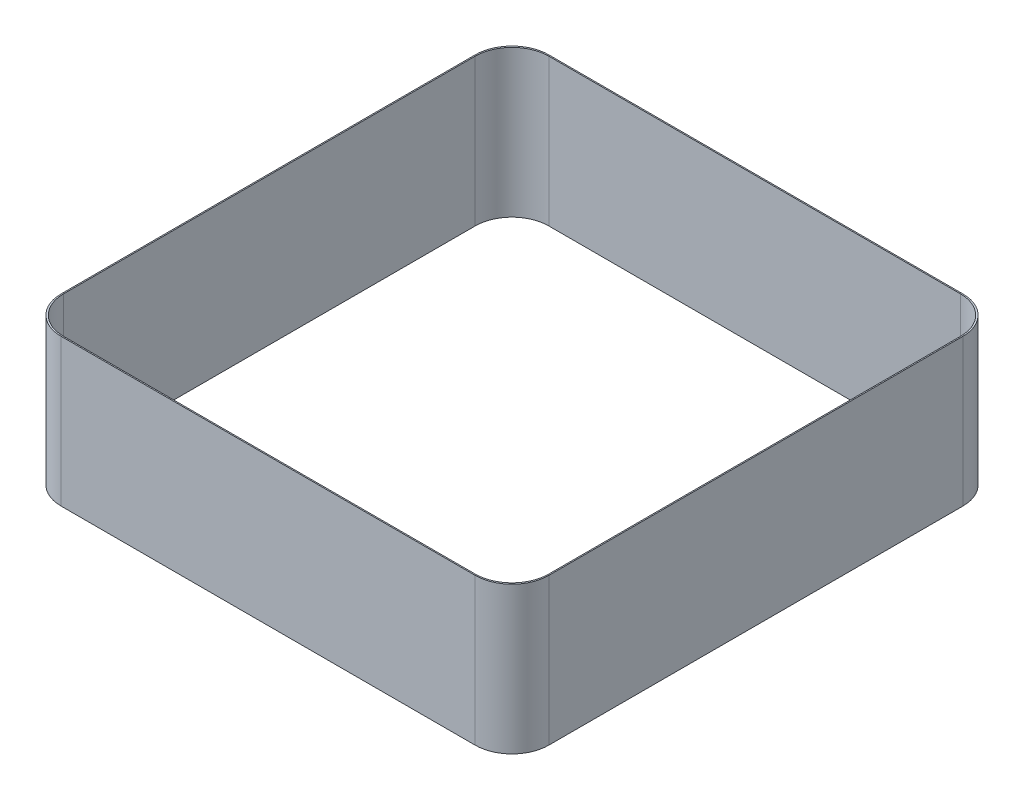
SolidWorks part; units mm, degrees
material "C110 COPPER"
ref_plane "Front Plane" through (0, 0, 0) normal (0, 0, 1) x (1, 0, 0)
ref_plane "Top Plane" through (0, 0, 0) normal (0, 1, 0) x (1, 0, 0)
ref_plane "Right Plane" through (0, 0, 0) normal (1, 0, 0) x (0, 0, -1)
sketch "Sketch2" plane through (0, 0, 0) normal (0, 1, 0) x (1, 0, 0)
  line L1 (-8.89, -10.4775) -> (8.89, -10.4775)
  line L2 (-10.4775, -8.89) -> (-10.4775, 8.89)
  line L3 (-8.89, 10.4775) -> (8.89, 10.4775)
  line L4 (10.4775, -8.89) -> (10.4775, 8.89)
  line L5 (-10.4775, -10.4775) -> (10.4775, 10.4775) construction
  line L6 (-10.4775, 10.4775) -> (10.4775, -10.4775) construction
  line L7 (-8.9408, -10.5283) -> (8.9408, -10.5283)
  line L8 (-10.5283, -8.9408) -> (-10.5283, 8.9408)
  line L9 (-8.9408, 10.5283) -> (8.9408, 10.5283)
  line L10 (10.5283, -8.9408) -> (10.5283, 8.9408)
  line L11 (-10.5283, -10.5283) -> (10.5283, 10.5283) construction
  line L12 (-10.5283, 10.5283) -> (10.5283, -10.5283) construction
  arc A0 (-8.9408, -10.5283) -> (-10.5283, -8.9408) centre (-8.9408, -8.9408) cw
  arc A1 (8.9408, -10.5283) -> (10.5283, -8.9408) centre (8.9408, -8.9408) ccw
  arc A2 (8.9408, 10.5283) -> (10.5283, 8.9408) centre (8.9408, 8.9408) cw
  arc A3 (-10.5283, 8.9408) -> (-8.9408, 10.5283) centre (-8.9408, 8.9408) cw
  arc A4 (-10.4775, 8.89) -> (-8.89, 10.4775) centre (-8.89, 8.89) cw
  arc A5 (-8.89, -10.4775) -> (-10.4775, -8.89) centre (-8.89, -8.89) cw
  arc A6 (8.89, -10.4775) -> (10.4775, -8.89) centre (8.89, -8.89) ccw
  arc A7 (8.89, 10.4775) -> (10.4775, 8.89) centre (8.89, 8.89) cw
  point P0 (0, 0)
  point P5 (0, 0)
  dimension "D3" = 1.5875
  dimension "D1" = 20.955
  dimension "D2" = 0.0508
extrude "Boss-Extrude1" add sketch "Sketch2" along normal blind 6.35
sketch "Sketch3" [suppressed] plane through (0, 6.35, 0) normal (0, 1, 0) x (1, 0, 0)
  line L0 (-8.9408, -10.5283) -> (8.9408, -10.5283) construction
  line L1 (-8.89, -10.4775) -> (8.89, -10.4775)
  line L2 (-8.89, -10.4775) -> (-8.89, -10.5283)
  line L3 (-8.89, -10.5283) -> (8.89, -10.5283)
  line L4 (8.89, -10.4775) -> (8.89, -10.5283)
extrude "Cut-Extrude1" [suppressed] cut sketch "Sketch3" against normal through all
